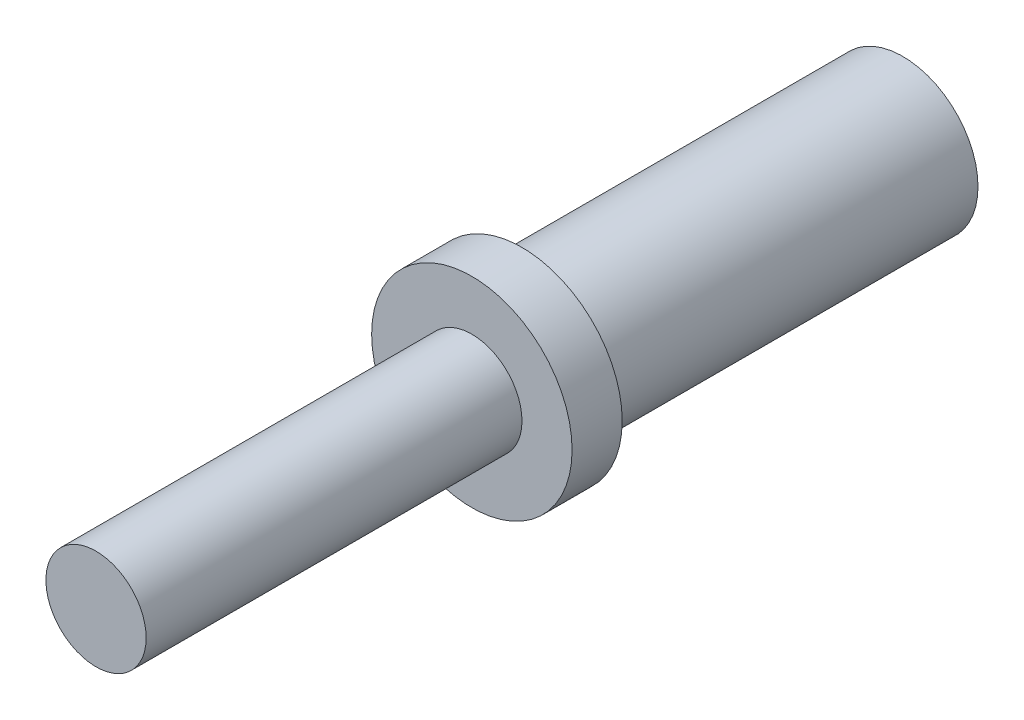
SolidWorks part; units mm, degrees
ref_plane "Front Plane" through (0, 0, 0) normal (0, 0, 1) x (1, 0, 0)
ref_plane "Top Plane" through (0, 0, 0) normal (0, 1, 0) x (1, 0, 0)
ref_plane "Right Plane" through (0, 0, 0) normal (1, 0, 0) x (0, 0, -1)
sketch "Sketch1" plane through (0, 0, 0) normal (1, 0, 0) x (0, 0, -1)
  line L0 (0, 0) -> (32.2, 0)
  line L1 (0, 0) -> (0, -2)
  line L2 (0, -2) -> (15, -2)
  line L3 (15, -2) -> (15, -4)
  line L4 (15, -4) -> (17, -4)
  line L5 (17, -4) -> (17, -3)
  line L6 (17, -3) -> (32.2, -3)
  line L7 (32.2, -3) -> (32.2, 0)
  dimension "D1" = 32.2
  dimension "D2" = 2
  dimension "D3" = 15
  dimension "D4" = 2
  dimension "D5" = 1
  dimension "D6" = 2
revolve "Revolve1" add sketch "Sketch1" angle 360 about L0
